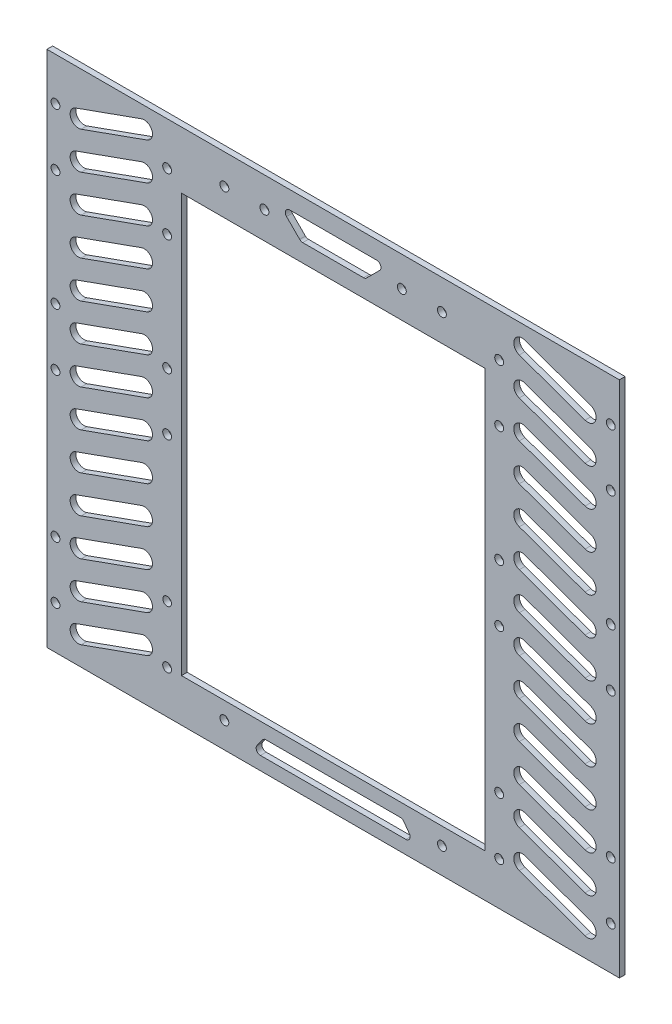
SolidWorks part; units mm, degrees
material "Thornel Mat VMA"
ref_plane "前视基准面" through (0, 0, 0) normal (0, 0, 1) x (1, 0, 0)
ref_plane "上视基准面" through (0, 0, 0) normal (0, 1, 0) x (1, 0, 0)
ref_plane "右视基准面" through (0, 0, 0) normal (1, 0, 0) x (0, 0, -1)
sketch "草图1" plane through (0, 0, 0) normal (0, 0, 1) x (1, 0, 0)
  line L0 (-119.8388, 0) -> (119.8388, 0) construction
  line L2 (-100, 62.5) -> (-100, -62.5)
  line L4 (100, 62.5) -> (100, -62.5)
  line L5 (-100, 62.5) -> (100, -62.5) construction
  line L6 (-100, -62.5) -> (100, 62.5) construction
  line L7 (-53, 70.5) -> (-53, -75.5)
  line L8 (53, -75.5) -> (53, 70.5)
  line L9 (-53, 70.5) -> (53, 70.5)
  line L10 (-53, -75.5) -> (53, -75.5)
  line L11 (-100, 62.5) -> (-100, 90.5)
  line L12 (-100, 90.5) -> (100, 90.5)
  line L13 (100, 90.5) -> (100, 62.5)
  line L14 (-100, -62.5) -> (-100, -90.5)
  line L15 (-100, -90.5) -> (100, -90.5)
  line L16 (100, -90.5) -> (100, -62.5)
  line L17 (-66, 83.264) -> (-89, 75.0316) construction
  line L18 (-65.0249, 80.5397) -> (-88.0249, 72.3074)
  line L19 (-66.9751, 85.9882) -> (-89.9751, 77.7559)
  line L20 (-66, 70.264) -> (-89, 62.0316) construction
  line L21 (-65.0249, 67.5397) -> (-88.0249, 59.3074)
  line L22 (-66.9751, 72.9882) -> (-89.9751, 64.7559)
  line L23 (-66, 57.264) -> (-89, 49.0316) construction
  line L24 (-65.0249, 54.5397) -> (-88.0249, 46.3074)
  line L25 (-66.9751, 59.9882) -> (-89.9751, 51.7559)
  line L26 (-66, 44.264) -> (-89, 36.0316) construction
  line L27 (-65.0249, 41.5397) -> (-88.0249, 33.3074)
  line L28 (-66.9751, 46.9882) -> (-89.9751, 38.7559)
  line L29 (-66, 31.264) -> (-89, 23.0316) construction
  line L30 (-65.0249, 28.5397) -> (-88.0249, 20.3074)
  line L31 (-66.9751, 33.9882) -> (-89.9751, 25.7559)
  line L32 (-66, 18.264) -> (-89, 10.0316) construction
  line L33 (-65.0249, 15.5397) -> (-88.0249, 7.3074)
  line L34 (-66.9751, 20.9882) -> (-89.9751, 12.7559)
  line L35 (-66, 5.264) -> (-89, -2.9684) construction
  line L36 (-65.0249, 2.5397) -> (-88.0249, -5.6926)
  line L37 (-66.9751, 7.9882) -> (-89.9751, -0.2441)
  line L38 (-66, -7.736) -> (-89, -15.9684) construction
  line L39 (-65.0249, -10.4603) -> (-88.0249, -18.6926)
  line L40 (-66.9751, -5.0118) -> (-89.9751, -13.2441)
  line L41 (-66, -20.736) -> (-89, -28.9684) construction
  line L42 (-65.0249, -23.4603) -> (-88.0249, -31.6926)
  line L43 (-66.9751, -18.0118) -> (-89.9751, -26.2441)
  line L44 (-66, -33.736) -> (-89, -41.9684) construction
  line L45 (-65.0249, -36.4603) -> (-88.0249, -44.6926)
  line L46 (-66.9751, -31.0118) -> (-89.9751, -39.2441)
  line L47 (-66, -46.736) -> (-89, -54.9684) construction
  line L48 (-65.0249, -49.4603) -> (-88.0249, -57.6926)
  line L49 (-66.9751, -44.0118) -> (-89.9751, -52.2441)
  line L50 (-66, -59.736) -> (-89, -67.9684) construction
  line L51 (-65.0249, -62.4603) -> (-88.0249, -70.6926)
  line L52 (-66.9751, -57.0118) -> (-89.9751, -65.2441)
  line L53 (-66, -72.736) -> (-89, -80.9684) construction
  line L54 (-65.0249, -75.4603) -> (-88.0249, -83.6926)
  line L55 (-66.9751, -70.0118) -> (-89.9751, -78.2441)
  line L56 (0, 141.91) -> (0, -159.2615) construction
  line L57 (66, -72.736) -> (89, -80.9684) construction
  line L58 (65.0249, -75.4603) -> (88.0249, -83.6926)
  line L59 (66.9751, -70.0118) -> (89.9751, -78.2441)
  line L60 (66, -59.736) -> (89, -67.9684) construction
  line L61 (65.0249, -62.4603) -> (88.0249, -70.6926)
  line L62 (66.9751, -57.0118) -> (89.9751, -65.2441)
  line L63 (66, -46.736) -> (89, -54.9684) construction
  line L64 (65.0249, -49.4603) -> (88.0249, -57.6926)
  line L65 (66.9751, -44.0118) -> (89.9751, -52.2441)
  line L66 (66, -33.736) -> (89, -41.9684) construction
  line L67 (65.0249, -36.4603) -> (88.0249, -44.6926)
  line L68 (66.9751, -31.0118) -> (89.9751, -39.2441)
  line L69 (66, -20.736) -> (89, -28.9684) construction
  line L70 (65.0249, -23.4603) -> (88.0249, -31.6926)
  line L71 (66.9751, -18.0118) -> (89.9751, -26.2441)
  line L72 (66, -7.736) -> (89, -15.9684) construction
  line L73 (65.0249, -10.4603) -> (88.0249, -18.6926)
  line L74 (66.9751, -5.0118) -> (89.9751, -13.2441)
  line L75 (66, 5.264) -> (89, -2.9684) construction
  line L76 (65.0249, 2.5397) -> (88.0249, -5.6926)
  line L77 (66.9751, 7.9882) -> (89.9751, -0.2441)
  line L78 (66, 18.264) -> (89, 10.0316) construction
  line L79 (65.0249, 15.5397) -> (88.0249, 7.3074)
  line L80 (66.9751, 20.9882) -> (89.9751, 12.7559)
  line L81 (66, 31.264) -> (89, 23.0316) construction
  line L82 (65.0249, 28.5397) -> (88.0249, 20.3074)
  line L83 (66.9751, 33.9882) -> (89.9751, 25.7559)
  line L84 (66, 44.264) -> (89, 36.0316) construction
  line L85 (65.0249, 41.5397) -> (88.0249, 33.3074)
  line L86 (66.9751, 46.9882) -> (89.9751, 38.7559)
  line L87 (66, 57.264) -> (89, 49.0316) construction
  line L88 (65.0249, 54.5397) -> (88.0249, 46.3074)
  line L89 (66.9751, 59.9882) -> (89.9751, 51.7559)
  line L90 (66, 70.264) -> (89, 62.0316) construction
  line L91 (65.0249, 67.5397) -> (88.0249, 59.3074)
  line L92 (66.9751, 72.9882) -> (89.9751, 64.7559)
  line L93 (66, 83.264) -> (89, 75.0316) construction
  line L94 (65.0249, 80.5397) -> (88.0249, 72.3074)
  line L95 (66.9751, 85.9882) -> (89.9751, 77.7559)
  line L96 (15.218, 84.306) -> (-15.218, 84.306)
  line L97 (-16.2787, 81.7453) -> (-11.6776, 77.1443)
  line L98 (-10.617, 76.7049) -> (10.617, 76.7049)
  line L99 (16.2787, 81.7453) -> (11.6776, 77.1443)
  line L100 (25.402, -85.8554) -> (-25.402, -85.8554)
  line L101 (-26.6201, -83.4801) -> (-24.6881, -80.7912)
  line L102 (-23.47, -80.1664) -> (23.47, -80.1664)
  line L103 (26.6201, -83.4801) -> (24.6881, -80.7912)
  circle A0 centre (-97, -75.5) radius 1.55
  circle A1 centre (-97, -55.5) radius 1.55
  circle A2 centre (-97, 75.5) radius 1.55
  circle A3 centre (-97, 55.5) radius 1.55
  circle A4 centre (-97, -5) radius 1.55
  circle A5 centre (-97, 15) radius 1.55
  circle A6 centre (97, 75.5) radius 1.55
  circle A7 centre (97, 55.5) radius 1.55
  circle A10 centre (97, -55.5) radius 1.55
  circle A11 centre (97, -75.5) radius 1.55
  circle A12 centre (-58, 75.5) radius 1.55
  circle A15 centre (-58, 55.5) radius 1.55
  circle A16 centre (-58, -55.5) radius 1.51
  circle A17 centre (-58, -75.5) radius 1.55
  circle A18 centre (58, 75.5) radius 1.55
  circle A19 centre (58, 55.5) radius 1.55
  circle A20 centre (58, -75.5) radius 1.55
  circle A21 centre (58, -55.5) radius 1.55
  circle A22 centre (-58, -5) radius 1.55
  circle A23 centre (-58, 15) radius 1.55
  circle A24 centre (97, 15) radius 1.55
  circle A25 centre (97, -5) radius 1.55
  circle A26 centre (58, 15) radius 1.55
  circle A27 centre (58, -5) radius 1.55
  circle A28 centre (-38, 80) radius 1.55
  circle A29 centre (-24, 80) radius 1.55
  circle A30 centre (24, 80) radius 1.55
  circle A31 centre (38, 80) radius 1.55
  circle A32 centre (-38, -81.5) radius 1.55
  circle A33 centre (38, -81.5) radius 1.55
  arc A34 (-65.0249, 80.5397) -> (-66.9751, 85.9882) centre (-66, 83.264) ccw
  arc A35 (-89.9751, 77.7559) -> (-88.0249, 72.3074) centre (-89, 75.0316) ccw
  arc A36 (-65.0249, 67.5397) -> (-66.9751, 72.9882) centre (-66, 70.264) ccw
  arc A37 (-89.9751, 64.7559) -> (-88.0249, 59.3074) centre (-89, 62.0316) ccw
  arc A38 (-65.0249, 54.5397) -> (-66.9751, 59.9882) centre (-66, 57.264) ccw
  arc A39 (-89.9751, 51.7559) -> (-88.0249, 46.3074) centre (-89, 49.0316) ccw
  arc A40 (-65.0249, 41.5397) -> (-66.9751, 46.9882) centre (-66, 44.264) ccw
  arc A41 (-89.9751, 38.7559) -> (-88.0249, 33.3074) centre (-89, 36.0316) ccw
  arc A42 (-65.0249, 28.5397) -> (-66.9751, 33.9882) centre (-66, 31.264) ccw
  arc A43 (-89.9751, 25.7559) -> (-88.0249, 20.3074) centre (-89, 23.0316) ccw
  arc A44 (-65.0249, 15.5397) -> (-66.9751, 20.9882) centre (-66, 18.264) ccw
  arc A45 (-89.9751, 12.7559) -> (-88.0249, 7.3074) centre (-89, 10.0316) ccw
  arc A46 (-65.0249, 2.5397) -> (-66.9751, 7.9882) centre (-66, 5.264) ccw
  arc A47 (-89.9751, -0.2441) -> (-88.0249, -5.6926) centre (-89, -2.9684) ccw
  arc A48 (-65.0249, -10.4603) -> (-66.9751, -5.0118) centre (-66, -7.736) ccw
  arc A49 (-89.9751, -13.2441) -> (-88.0249, -18.6926) centre (-89, -15.9684) ccw
  arc A50 (-65.0249, -23.4603) -> (-66.9751, -18.0118) centre (-66, -20.736) ccw
  arc A51 (-89.9751, -26.2441) -> (-88.0249, -31.6926) centre (-89, -28.9684) ccw
  arc A52 (-65.0249, -36.4603) -> (-66.9751, -31.0118) centre (-66, -33.736) ccw
  arc A53 (-89.9751, -39.2441) -> (-88.0249, -44.6926) centre (-89, -41.9684) ccw
  arc A54 (-65.0249, -49.4603) -> (-66.9751, -44.0118) centre (-66, -46.736) ccw
  arc A55 (-89.9751, -52.2441) -> (-88.0249, -57.6926) centre (-89, -54.9684) ccw
  arc A56 (-65.0249, -62.4603) -> (-66.9751, -57.0118) centre (-66, -59.736) ccw
  arc A57 (-89.9751, -65.2441) -> (-88.0249, -70.6926) centre (-89, -67.9684) ccw
  arc A58 (-65.0249, -75.4603) -> (-66.9751, -70.0118) centre (-66, -72.736) ccw
  arc A59 (-89.9751, -78.2441) -> (-88.0249, -83.6926) centre (-89, -80.9684) ccw
  arc A60 (65.0249, -75.4603) -> (66.9751, -70.0118) centre (66, -72.736) cw
  arc A61 (89.9751, -78.2441) -> (88.0249, -83.6926) centre (89, -80.9684) cw
  arc A62 (65.0249, -62.4603) -> (66.9751, -57.0118) centre (66, -59.736) cw
  arc A63 (89.9751, -65.2441) -> (88.0249, -70.6926) centre (89, -67.9684) cw
  arc A64 (65.0249, -49.4603) -> (66.9751, -44.0118) centre (66, -46.736) cw
  arc A65 (89.9751, -52.2441) -> (88.0249, -57.6926) centre (89, -54.9684) cw
  arc A66 (65.0249, -36.4603) -> (66.9751, -31.0118) centre (66, -33.736) cw
  arc A67 (89.9751, -39.2441) -> (88.0249, -44.6926) centre (89, -41.9684) cw
  arc A68 (65.0249, -23.4603) -> (66.9751, -18.0118) centre (66, -20.736) cw
  arc A69 (89.9751, -26.2441) -> (88.0249, -31.6926) centre (89, -28.9684) cw
  arc A70 (65.0249, -10.4603) -> (66.9751, -5.0118) centre (66, -7.736) cw
  arc A71 (89.9751, -13.2441) -> (88.0249, -18.6926) centre (89, -15.9684) cw
  arc A72 (65.0249, 2.5397) -> (66.9751, 7.9882) centre (66, 5.264) cw
  arc A73 (89.9751, -0.2441) -> (88.0249, -5.6926) centre (89, -2.9684) cw
  arc A74 (65.0249, 15.5397) -> (66.9751, 20.9882) centre (66, 18.264) cw
  arc A75 (89.9751, 12.7559) -> (88.0249, 7.3074) centre (89, 10.0316) cw
  arc A76 (65.0249, 28.5397) -> (66.9751, 33.9882) centre (66, 31.264) cw
  arc A77 (89.9751, 25.7559) -> (88.0249, 20.3074) centre (89, 23.0316) cw
  arc A78 (65.0249, 41.5397) -> (66.9751, 46.9882) centre (66, 44.264) cw
  arc A79 (89.9751, 38.7559) -> (88.0249, 33.3074) centre (89, 36.0316) cw
  arc A80 (65.0249, 54.5397) -> (66.9751, 59.9882) centre (66, 57.264) cw
  arc A81 (89.9751, 51.7559) -> (88.0249, 46.3074) centre (89, 49.0316) cw
  arc A82 (65.0249, 67.5397) -> (66.9751, 72.9882) centre (66, 70.264) cw
  arc A83 (89.9751, 64.7559) -> (88.0249, 59.3074) centre (89, 62.0316) cw
  arc A84 (65.0249, 80.5397) -> (66.9751, 85.9882) centre (66, 83.264) cw
  arc A85 (89.9751, 77.7559) -> (88.0249, 72.3074) centre (89, 75.0316) cw
  arc A86 (-11.6776, 77.1443) -> (-10.617, 76.7049) centre (-10.617, 78.2049) ccw
  arc A87 (-16.2787, 81.7453) -> (-15.218, 84.306) centre (-15.218, 82.806) cw
  arc A88 (11.6776, 77.1443) -> (10.617, 76.7049) centre (10.617, 78.2049) cw
  arc A89 (16.2787, 81.7453) -> (15.218, 84.306) centre (15.218, 82.806) ccw
  arc A90 (-25.402, -85.8554) -> (-26.6201, -83.4801) centre (-25.402, -84.3554) cw
  arc A91 (-24.6881, -80.7912) -> (-23.47, -80.1664) centre (-23.47, -81.6664) cw
  arc A92 (25.402, -85.8554) -> (26.6201, -83.4801) centre (25.402, -84.3554) ccw
  arc A93 (24.6881, -80.7912) -> (23.47, -80.1664) centre (23.47, -81.6664) ccw
  point P0 (0, 0)
  point P9 (0, 0)
  point P79 (-77.5, 79.1478)
  point P87 (-77.5, 66.1478)
  point P94 (-77.5, 53.1478)
  point P101 (-77.5, 40.1478)
  point P108 (-77.5, 27.1478)
  point P115 (-77.5, 14.1478)
  point P122 (-77.5, 1.1478)
  point P129 (-77.5, -11.8522)
  point P136 (-77.5, -24.8522)
  point P143 (-77.5, -37.8522)
  point P150 (-77.5, -50.8522)
  point P157 (-77.5, -63.8522)
  point P164 (-77.5, -76.8522)
  point P172 (77.5, -76.8522)
  point P179 (77.5, -63.8522)
  point P186 (77.5, -50.8522)
  point P193 (77.5, -37.8522)
  point P200 (77.5, -24.8522)
  point P207 (77.5, -11.8522)
  point P214 (77.5, 1.1478)
  point P221 (77.5, 14.1478)
  point P228 (77.5, 27.1478)
  point P235 (77.5, 40.1478)
  point P242 (77.5, 53.1478)
  point P249 (77.5, 66.1478)
  point P256 (77.5, 79.1478)
  point P270 (0, 76.7049)
  point P275 (0, 84.306)
  point P284 (0, -85.8554)
  point P289 (0, -80.1664)
  dimension "D11" = 3
  dimension "D16" = 42
  dimension "D17" = 42
  dimension "D18" = 47
  dimension "D22" = 9.5
  dimension "D30" = 15
  dimension "D34" = 28
  dimension "D52" = 1.5
  dimension "D53" = 1.5
  dimension "D1" = 200
  dimension "D2" = 125
  dimension "D4" = 20
  dimension "D5" = 3
  dimension "D6" = 3
  dimension "D7" = 3
  dimension "D8" = 3
  dimension "D9" = 15
  dimension "D10" = 20
  dimension "D12" = 3
  dimension "D13" = 5
  dimension "D14" = 15
  dimension "D15" = 3
  dimension "D19" = 47
  dimension "D20" = 15
  dimension "D21" = 20
  dimension "D23" = 9.5
  dimension "D24" = 9.5
  dimension "D25" = 9.5
  dimension "D26" = 14
  dimension "D27" = 14
  dimension "D28" = 15
  dimension "D29" = 15
  dimension "D31" = 15
  dimension "D32" = 15
  dimension "D33" = 20
  dimension "D35" = 28
  dimension "D36" = 15
  dimension "D37" = 20
  dimension "D38" = 20
  dimension "D39" = 15
  dimension "D40" = 15
  dimension "D41" = 20
  dimension "D42" = 20
  dimension "D43" = 15
  dimension "D44" = 15
  dimension "D45" = 6
  dimension "D46" = 6
  dimension "D47" = 15
  dimension "D48" = 20
  dimension "D49" = 11
  dimension "D50" = 13
  dimension "D51" = 13
extrude "凸台-拉伸1" add sketch "草图1" along normal blind 2
